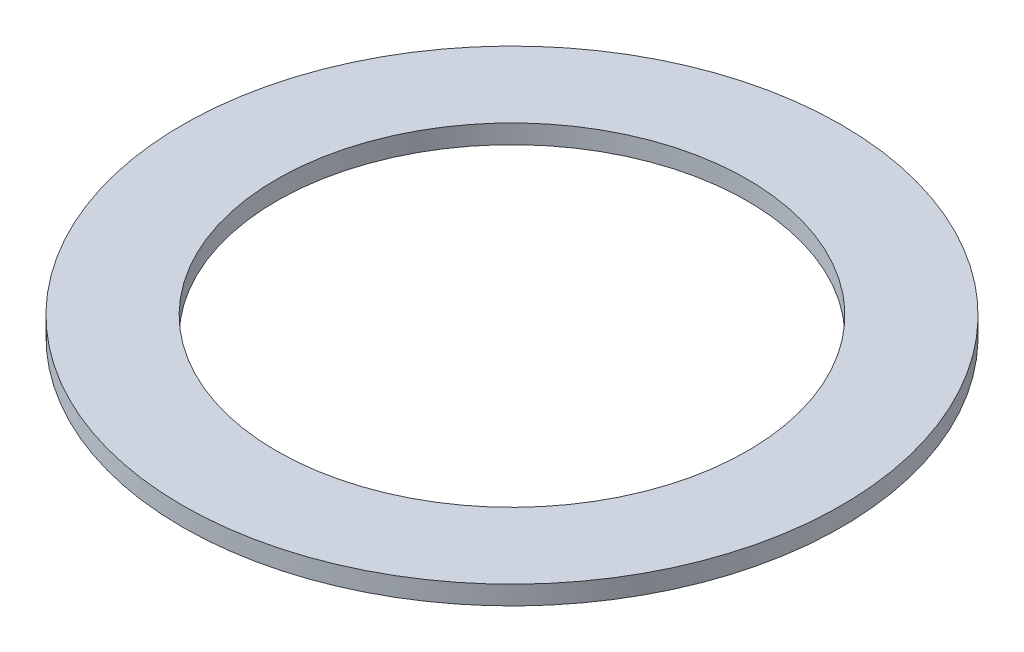
SolidWorks part; units mm, degrees
ref_plane "Front Plane" through (0, 0, 0) normal (0, 0, 1) x (1, 0, 0)
ref_plane "Top Plane" through (0, 0, 0) normal (0, 1, 0) x (1, 0, 0)
ref_plane "Right Plane" through (0, 0, 0) normal (1, 0, 0) x (0, 0, -1)
sketch "Sketch1" plane through (0, 0, 0) normal (0, 1, 0) x (1, 0, 0)
  circle A0 centre (0, 0) radius 3.5
  dimension "OD" = 7
extrude "Boss-Extrude1" add sketch "Sketch1" along normal blind 0.2
sketch "Sketch5" plane through (0, 0.2, 0) normal (0, 1, 0) x (-1, 0, 0)
  circle A0 centre (0, 0) radius 2.5
  dimension "ID" = 5
extrude "Cut-Extrude1" cut sketch "Sketch5" against normal through all
